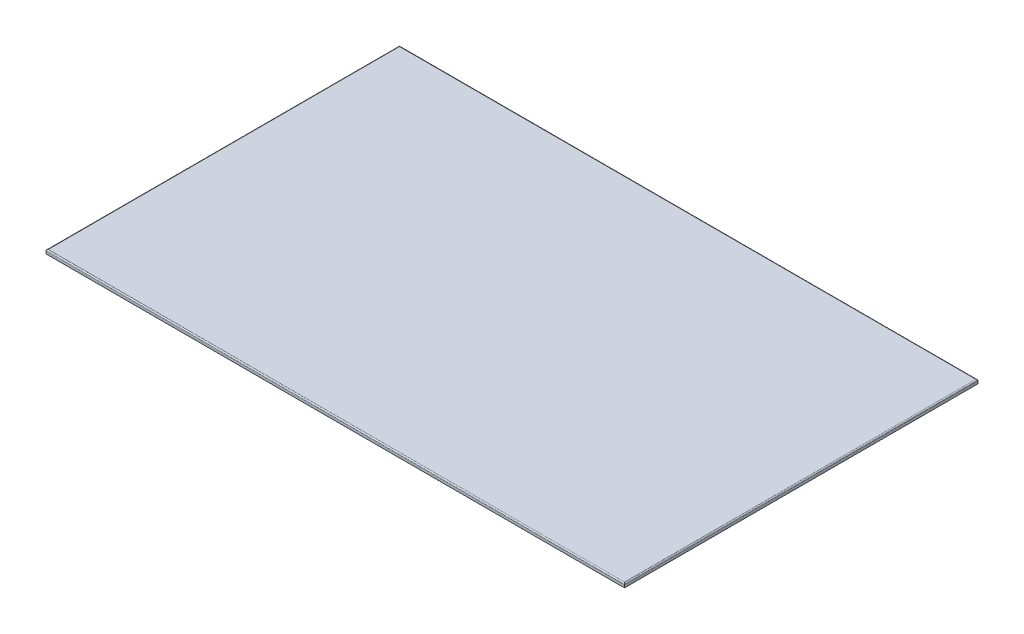
SolidWorks part; units mm, degrees
ref_plane "Ebene vorne" through (0, 0, 0) normal (0, 0, 1) x (1, 0, 0)
ref_plane "Ebene oben" through (0, 0, 0) normal (0, 1, 0) x (1, 0, 0)
ref_plane "Ebene rechts" through (0, 0, 0) normal (1, 0, 0) x (0, 0, -1)
sketch "Sketch1" plane through (0, 0, 0) normal (0, 1, 0) x (1, 0, 0)
  line L1 (-450, -275) -> (450, -275)
  line L2 (-450, -275) -> (-450, 275)
  line L3 (-450, 275) -> (450, 275)
  line L4 (450, -275) -> (450, 275)
  line L5 (-450, -275) -> (450, 275) construction
  line L6 (-450, 275) -> (450, -275) construction
  point P0 (0, 0)
  dimension "D1" = 550
  dimension "D2" = 900
extrude "Boss-Extrude1" add sketch "Sketch1" along normal blind 6
fillet "Fillet1" radius 1.75 4 edges at (0, 6, -275) (450, 6, 0) (-450, 6, 0) (0, 6, 275)
